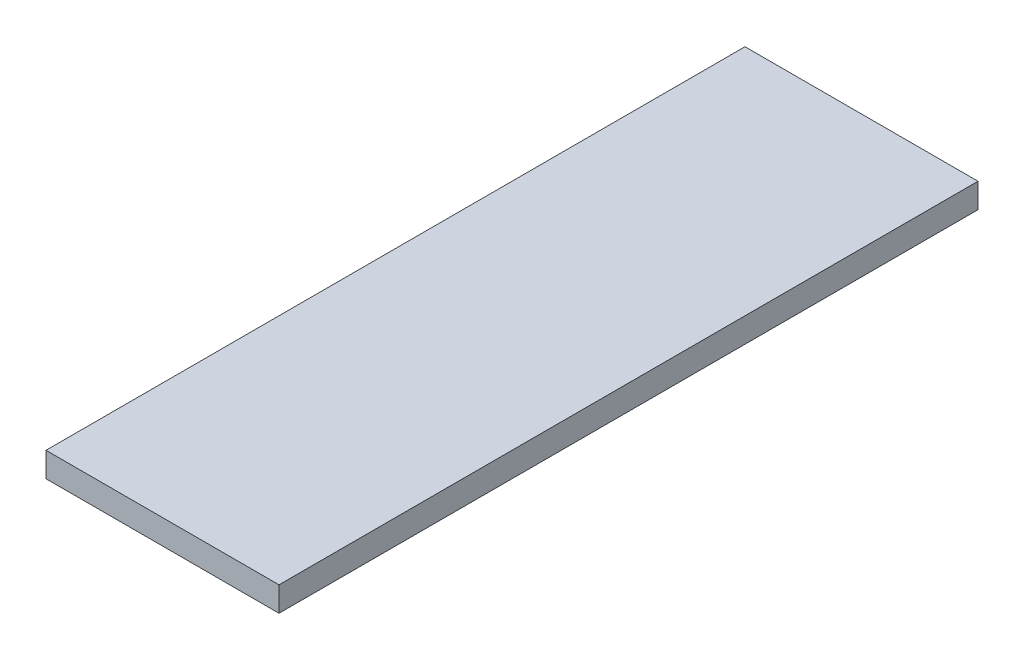
SolidWorks part; units mm, degrees
ref_plane "Front Plane" through (0, 0, 0) normal (0, 0, 1) x (1, 0, 0)
ref_plane "Top Plane" through (0, 0, 0) normal (0, 1, 0) x (1, 0, 0)
ref_plane "Right Plane" through (0, 0, 0) normal (1, 0, 0) x (0, 0, -1)
sketch "Sketch1" plane through (0, 0, 0) normal (0, 1, 0) x (1, 0, 0)
  line L1 (0, 0) -> (30, 0)
  line L2 (0, 0) -> (0, 90)
  line L3 (0, 90) -> (30, 90)
  line L4 (30, 0) -> (30, 90)
  dimension "D1" = 30
  dimension "D2" = 90
extrude "Boss-Extrude1" add sketch "Sketch1" along normal blind 3.175
